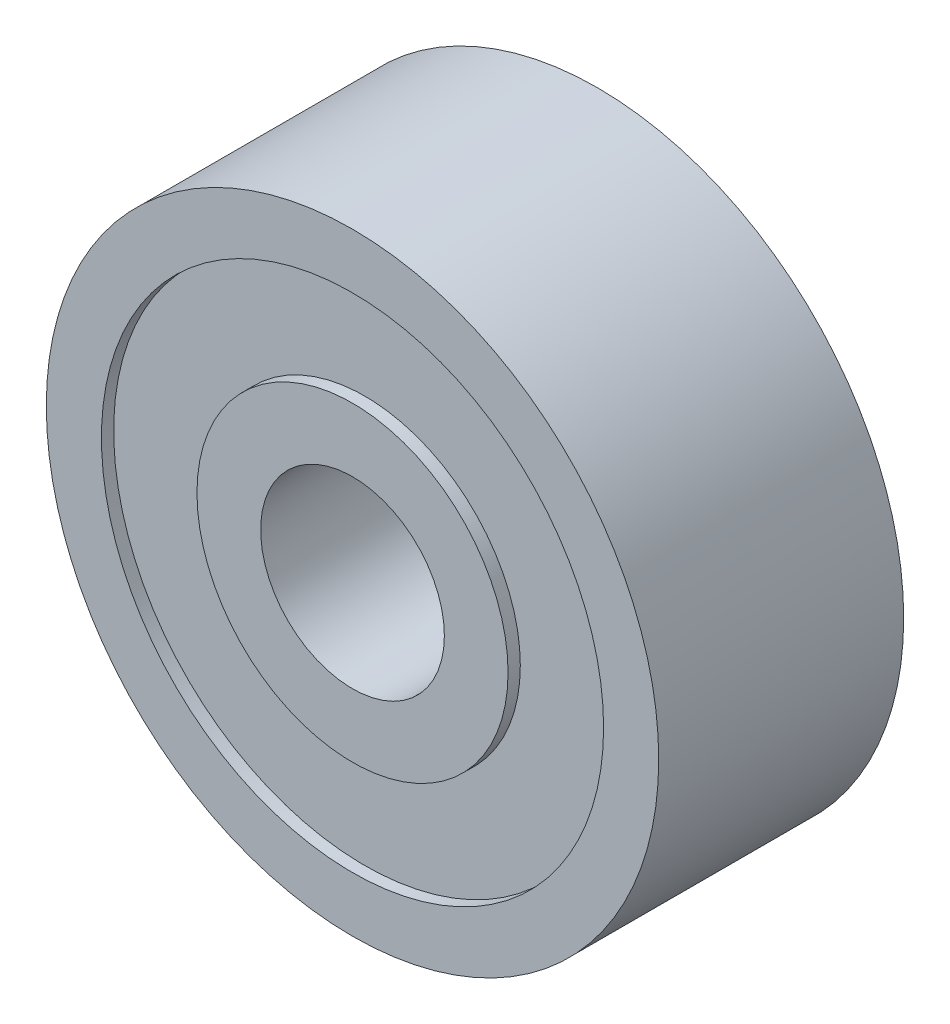
SolidWorks part; units mm, degrees
material "鉻不鏽鋼"
ref_plane "前基準面" through (0, 0, 0) normal (0, 0, 1) x (1, 0, 0)
ref_plane "上基準面" through (0, 0, 0) normal (0, 1, 0) x (1, 0, 0)
ref_plane "右基準面" through (0, 0, 0) normal (1, 0, 0) x (0, 0, -1)
sketch "草圖1" plane through (0, 0, 0) normal (0, 0, 1) x (1, 0, 0)
  circle A0 centre (0, 0) radius 5
  dimension "D1" = 10
extrude "填料-伸長1" add sketch "草圖1" along normal mid plane 4
sketch "草圖2" plane through (0, 0, 2) normal (0, 0, 1) x (1, 0, 0)
  circle A0 centre (0, 0) radius 1.5
  dimension "D1" = 3
extrude "除料-伸長1" cut sketch "草圖2" against normal through all
sketch "草圖3" plane through (0, 0, 2) normal (0, 0, 1) x (1, 0, 0)
  circle A0 centre (0, 0) radius 2.54
  circle A1 centre (0, 0) radius 4.1
  dimension "D1" = 8.2
  dimension "D2" = 5.08
extrude "除料-伸長2" cut sketch "草圖3" against normal blind 0.2
mirror "鏡射1" about plane through (0, 0, 0) normal (0, 0, 1) of "除料-伸長2"
